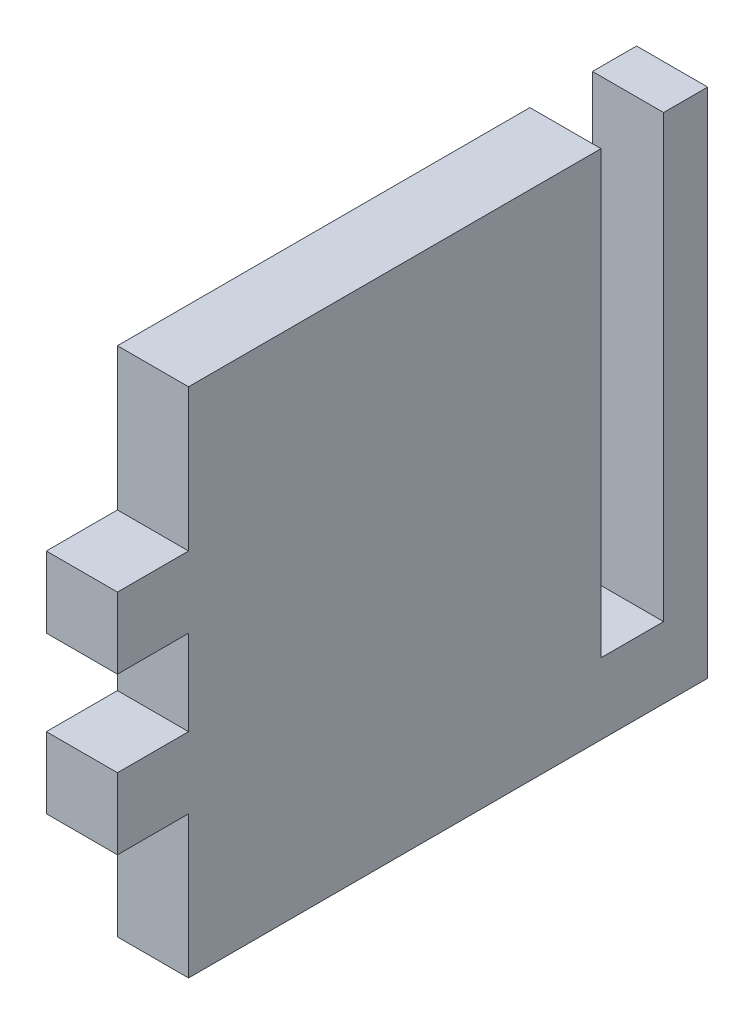
SolidWorks part; units mm, degrees
ref_plane "Front Plane" through (0, 0, 0) normal (0, 0, 1) x (1, 0, 0)
ref_plane "Top Plane" through (0, 0, 0) normal (0, 1, 0) x (1, 0, 0)
ref_plane "Right Plane" through (0, 0, 0) normal (1, 0, 0) x (0, 0, -1)
sketch "Sketch1" plane through (0, 0, 0) normal (1, 0, 0) x (0, 0, -1)
  line L1 (0, 0) -> (52.705, 0)
  line L2 (0, 0) -> (0, 45.72)
  line L3 (0, 45.72) -> (52.705, 45.72)
  line L4 (52.705, 0) -> (52.705, 45.72)
  dimension "D1" = 45.72
  dimension "D2" = 52.705
extrude "Boss-Extrude1" add sketch "Sketch1" along normal blind 6.35
sketch "Sketch2" plane through (6.35, 0, 0) normal (1, 0, 0) x (0, 0, -1)
  line L0 (0, 45.72) -> (0, 0) construction
  line L1 (0, 45.72) -> (6.35, 45.72)
  line L2 (0, 45.72) -> (0, 33.02)
  line L3 (0, 33.02) -> (6.35, 33.02)
  line L4 (6.35, 45.72) -> (6.35, 33.02)
  line L5 (0, 12.7) -> (6.35, 12.7)
  line L6 (0, 12.7) -> (0, 0)
  line L7 (0, 0) -> (6.35, 0)
  line L8 (6.35, 12.7) -> (6.35, 0)
  line L9 (0, 0) -> (52.705, 0) construction
  line L10 (52.705, 45.72) -> (0, 45.72) construction
  line L11 (0, 26.67) -> (6.35, 26.67)
  line L12 (0, 26.67) -> (0, 19.05)
  line L13 (0, 19.05) -> (6.35, 19.05)
  line L14 (6.35, 26.67) -> (6.35, 19.05)
  line L15 (43.18, 45.72) -> (48.768, 45.72)
  line L16 (43.18, 45.72) -> (43.18, 6.35)
  line L17 (43.18, 6.35) -> (48.768, 6.35)
  line L18 (48.768, 45.72) -> (48.768, 6.35)
  dimension "D1" = 12.7
  dimension "D2" = 6.35
  dimension "D3" = 6.35
  dimension "D4" = 12.7
  dimension "D5" = 6.35
  dimension "D6" = 43.18
  dimension "D7" = 5.588
  dimension "D8" = 6.35
extrude "Cut-Extrude1" cut sketch "Sketch2" against normal through all
